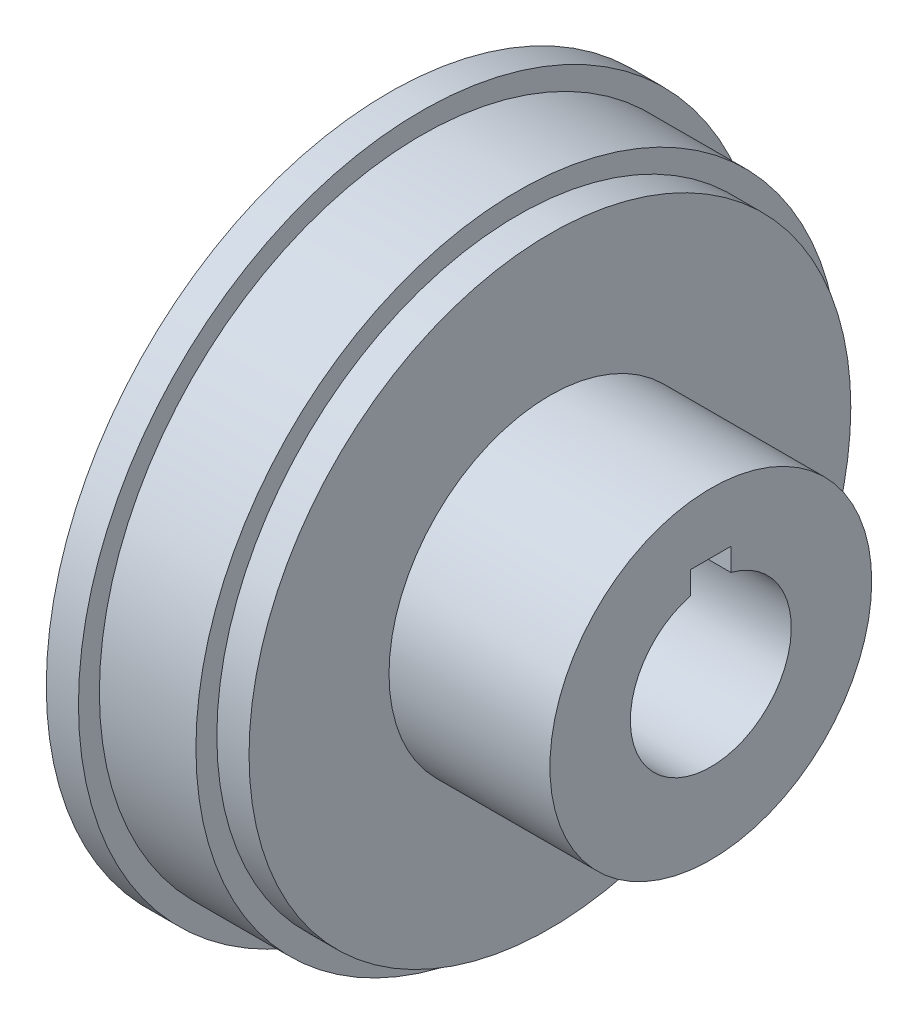
SolidWorks part; units mm, degrees
material "Plain Carbon Steel"
ref_plane "Front Plane" through (0, 0, 0) normal (0, 0, 1) x (1, 0, 0)
ref_plane "Top Plane" through (0, 0, 0) normal (0, 1, 0) x (1, 0, 0)
ref_plane "Right Plane" through (0, 0, 0) normal (1, 0, 0) x (0, 0, -1)
sketch "Sketch1" plane through (0, 0, 0) normal (1, 0, 0) x (0, 0, -1)
  line L0 (0, 7.9375) -> (0, 4.7625) construction
  line L1 (-1.5875, 7.9375) -> (1.5875, 7.9375)
  line L2 (-1.5875, 7.9375) -> (-1.5875, 4.7625)
  line L3 (-1.5875, 4.7625) -> (1.5875, 4.7625)
  line L4 (1.5875, 7.9375) -> (1.5875, 4.7625)
  line L5 (0, 4.7625) -> (1.5875, 6.35) construction
  line L6 (1.5875, 6.35) -> (-1.5875, 6.35) construction
  line L7 (0, 4.7625) -> (0, 0) construction
  circle A0 centre (0, 0) radius 6.35
  circle A1 centre (0, 0) radius 22.225
  dimension "D1" = 6.35
  dimension "D2" = 1.5875
  dimension "D3" = 3.175
extrude "Boss-Extrude1" add sketch "Sketch1" along normal blind 25.4 contours A1 A0 L2 L1 L4
sketch "Sketch2" plane through (0, 0, 0) normal (-1, 0, 0) x (0, 0, 1)
  circle A0 centre (0, 0) radius 10.9141
  circle A1 centre (0, 0) radius 25.4
extrude "Boss-Extrude2" add sketch "Sketch2" against normal blind 12.7
sketch "Sketch3" plane through (25.4, 0, 0) normal (1, 0, 0) x (0, 0, -1)
  circle A0 centre (0, 0) radius 12.7
  circle A1 centre (0, 0) radius 25.4
extrude "Cut-Extrude1" cut sketch "Sketch3" against normal up to surface (12.7 mm away) up to face at (12.7, 0, 25.4)
sketch "Sketch5" plane through (0, 0, 0) normal (-1, 0, 0) x (0, 0, 1)
  circle A0 centre (0, 0) radius 27.051
  circle A1 centre (0, 0) radius 25.4
extrude "Boss-Extrude3" add sketch "Sketch5" against normal blind 2.54
sketch "Sketch6" plane through (12.7, 0, 0) normal (1, 0, 0) x (0, 0, -1)
  circle A0 centre (0, 0) radius 23.749
  circle A1 centre (0, 0) radius 25.4
extrude "Cut-Extrude3" cut sketch "Sketch6" against normal blind 2.54
